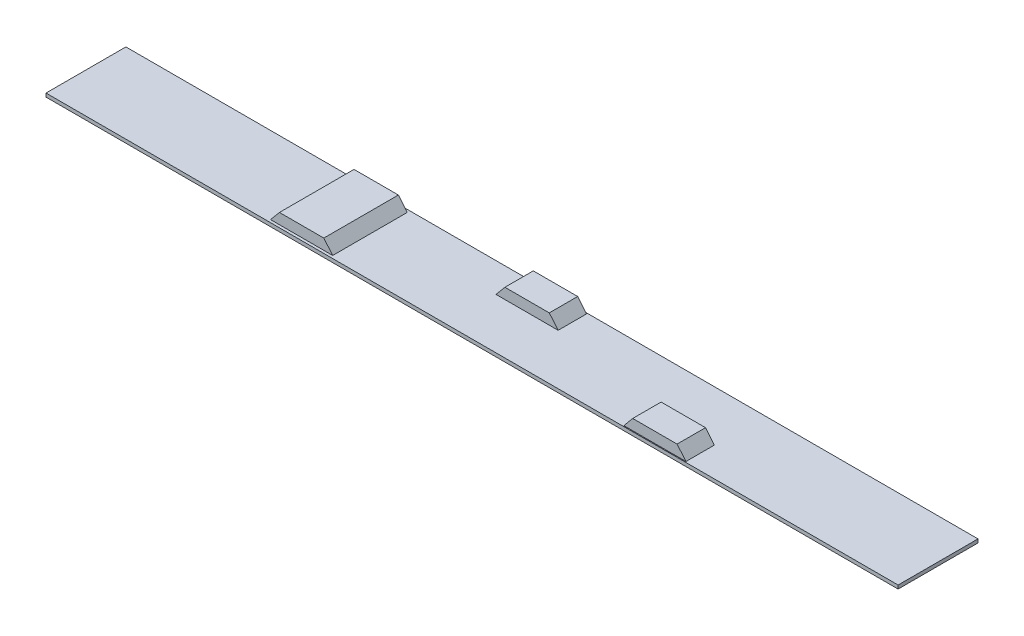
SolidWorks part; units mm, degrees
ref_plane "Front Plane" through (0, 0, 0) normal (0, 0, 1) x (1, 0, 0)
ref_plane "Top Plane" through (0, 0, 0) normal (0, 1, 0) x (1, 0, 0)
ref_plane "Right Plane" through (0, 0, 0) normal (1, 0, 0) x (0, 0, -1)
sketch "Sketch1" plane through (0, 0, 0) normal (0, 1, 0) x (1, 0, 0)
  line L1 (-1200, 112.5) -> (1200, 112.5)
  line L2 (-1200, 112.5) -> (-1200, -112.5)
  line L3 (-1200, -112.5) -> (1200, -112.5)
  line L4 (1200, 112.5) -> (1200, -112.5)
  line L5 (-1200, 112.5) -> (1200, -112.5) construction
  line L6 (-1200, -112.5) -> (1200, 112.5) construction
  point P0 (0, 0)
  dimension "D1" = 2400
  dimension "D2" = 225
extrude "Boss-Extrude1" add sketch "Sketch1" along normal blind 10
sketch "Sketch2" plane through (0, 0, 0) normal (0, 0, 1) x (1, 0, 0)
  line L0 (425, 10) -> (450, 40)
  line L1 (-1200, 10) -> (1200, 10) construction
  line L2 (450, 40) -> (575, 40)
  line L3 (575, 40) -> (600, 10)
  line L4 (600, 10) -> (425, 10)
  line L5 (1200, 10) -> (1200, 0) construction
  point P4 (512.5, 40)
  point P7 (512.5, 10)
  dimension "D1" = 175
  dimension "D2" = 125
  dimension "D3" = 30
  dimension "D4" = 600
extrude "Boss-Extrude2" add sketch "Sketch2" along normal blind 80 from offset 30
sketch "Sketch4" plane through (0, 0, 0) normal (0, 0, 1) x (1, 0, 0)
  line L0 (-50, 40) -> (-75, 10)
  line L1 (75, 40) -> (-50, 40)
  line L2 (100, 10) -> (75, 40)
  line L3 (-75, 10) -> (100, 10)
  line L4 (450, 40) -> (425, 10)
  line L5 (575, 40) -> (450, 40)
  line L6 (600, 10) -> (575, 40)
  line L7 (425, 10) -> (600, 10)
  line L8 (450, 40) -> (425, 10) construction
  line L9 (575, 40) -> (450, 40) construction
  line L10 (600, 10) -> (575, 40) construction
  line L11 (425, 10) -> (600, 10) construction
  dimension "D1" = 0
  dimension "D2" = 2
extrude "Boss-Extrude3" add sketch "Sketch4" against normal blind 80 from offset 30 offset against normal yes
sketch "Sketch5" plane through (0, 0, 0) normal (0, 0, 1) x (1, 0, 0)
  line L0 (-550, 40) -> (-575, 10)
  line L1 (-575, 10) -> (-400, 10)
  line L2 (-400, 10) -> (-425, 40)
  line L3 (-425, 40) -> (-550, 40)
  line L4 (-50, 40) -> (-75, 10)
  line L5 (-75, 10) -> (100, 10)
  line L6 (100, 10) -> (75, 40)
  line L7 (75, 40) -> (-50, 40)
  line L8 (-50, 40) -> (-75, 10) construction
  line L9 (-75, 10) -> (100, 10) construction
  line L10 (100, 10) -> (75, 40) construction
  line L11 (75, 40) -> (-50, 40) construction
  dimension "D1" = 0
  dimension "D2" = 2
extrude "Boss-Extrude4" add sketch "Sketch5" along normal blind 105 and the other way blind 105
